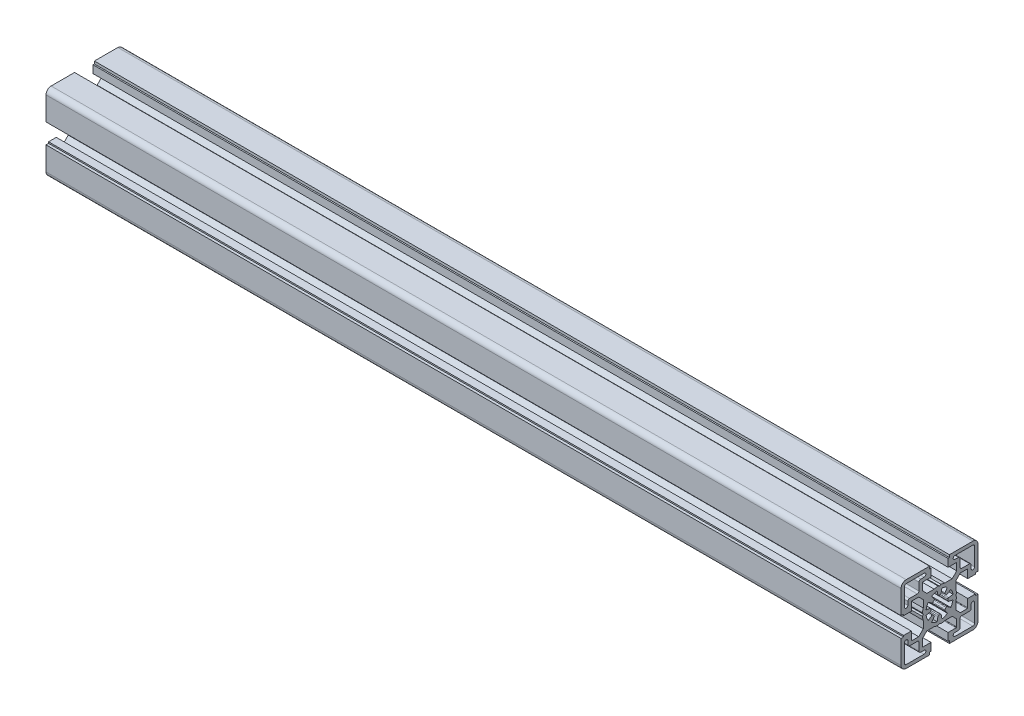
SolidWorks part; units mm, degrees
ref_plane "Спереди" through (0, 0, 0) normal (0, 0, 1) x (1, 0, 0)
ref_plane "Сверху" through (0, 0, 0) normal (0, 1, 0) x (1, 0, 0)
ref_plane "Справа" through (0, 0, 0) normal (1, 0, 0) x (0, 0, -1)
sketch "Эскиз2" plane through (0, 0, 0) normal (1, 0, 0) x (0, 0, -1)
  line L0 (-0.9511, 5.394) -> (-1.3892, 7.8785)
  line L1 (-3.1416, 4.4867) -> (-4.5886, 6.5532)
  line L2 (-4.4867, 3.1416) -> (-6.5532, 4.5886)
  line L3 (7.8785, -1.3892) -> (5.394, -0.9511)
  line L4 (-5.394, 0.9511) -> (-7.8785, 1.3892)
  line L5 (16.5, 5) -> (21, 5)
  line L6 (-21, 5) -> (-16.5, 5)
  line L7 (21, 5.8) -> (22.5, 5.8)
  line L8 (-22.5, 5.8) -> (-21, 5.8)
  line L9 (3.1225, 9.5) -> (7.3787, 9.5)
  line L10 (-7.3787, 9.5) -> (-3.1225, 9.5)
  line L11 (12.1713, 10.05) -> (16.2, 10.05)
  line L12 (-16.2, 10.05) -> (-12.1713, 10.05)
  line L13 (-17.5, 12) -> (-13, 12)
  line L14 (5, 16.5) -> (9.75, 16.5)
  line L15 (-9.75, 16.5) -> (-5, 16.5)
  line L16 (-19.5, 20.5) -> (-9, 20.5)
  line L17 (5, 21) -> (5.8, 21)
  line L18 (-5.8, 21) -> (-5, 21)
  line L19 (5.8, 22.5) -> (19.5, 22.5)
  line L20 (-19.5, 22.5) -> (-5.8, 22.5)
  line L21 (-7.8785, -1.3892) -> (-5.394, -0.9511)
  line L22 (5.394, 0.9511) -> (7.8785, 1.3892)
  line L23 (4.4867, 3.1416) -> (6.5532, 4.5886)
  line L24 (3.1416, 4.4867) -> (4.5886, 6.5532)
  line L25 (0.9511, 5.394) -> (1.3892, 7.8785)
  line L26 (-22.5, 5.8) -> (-22.5, 19.5)
  line L27 (-21, 5) -> (-21, 5.8)
  line L28 (-20.5, 9) -> (-20.5, 19.5)
  line L29 (-16.5, 5) -> (-16.5, 9.75)
  line L30 (-12, 13) -> (-12, 17.5)
  line L31 (-5.8, 21) -> (-5.8, 22.5)
  line L32 (-5, 16.5) -> (-5, 21)
  line L33 (5, 16.5) -> (5, 21)
  line L34 (5.8, 21) -> (5.8, 22.5)
  line L35 (9.5, 3.1225) -> (9.5, 7.3787)
  line L36 (10.05, 12.1713) -> (10.05, 16.2)
  line L37 (16.5, 5) -> (16.5, 9.75)
  line L38 (21, 5) -> (21, 5.8)
  line L39 (22.5, 5.8) -> (22.5, 19.5)
  line L40 (1.3892, -7.8785) -> (0.9511, -5.394)
  line L41 (4.5886, -6.5532) -> (3.1416, -4.4867)
  line L42 (6.5532, -4.5886) -> (4.4867, -3.1416)
  line L43 (-7.3787, -9.5) -> (-3.1225, -9.5)
  line L44 (3.1225, -9.5) -> (7.3787, -9.5)
  line L45 (-6.5532, -4.5886) -> (-4.4867, -3.1416)
  line L46 (-4.5886, -6.5532) -> (-3.1416, -4.4867)
  line L47 (-1.3892, -7.8785) -> (-0.9511, -5.394)
  line L48 (-9.5, -7.3787) -> (-9.5, -3.1225)
  line L49 (9.5, -7.3787) -> (9.5, -3.1225)
  line L50 (-22.5, -5.8) -> (-21, -5.8)
  line L51 (-21, -5) -> (-16.5, -5)
  line L52 (-21, -5.8) -> (-21, -5)
  line L53 (-16.5, -9.75) -> (-16.5, -5)
  line L54 (-22.5, -19.5) -> (-22.5, -5.8)
  line L55 (21, -5.8) -> (22.5, -5.8)
  line L56 (16.5, -5) -> (21, -5)
  line L57 (21, -5.8) -> (21, -5)
  line L58 (16.5, -9.75) -> (16.5, -5)
  line L59 (12.1713, -10.05) -> (16.2, -10.05)
  line L60 (22.5, -19.5) -> (22.5, -5.8)
  line L61 (-16.2, -10.05) -> (-12.1713, -10.05)
  line L62 (5, -16.5) -> (9.75, -16.5)
  line L63 (-9.75, -16.5) -> (-5, -16.5)
  line L64 (5, -21) -> (5.8, -21)
  line L65 (-5.8, -21) -> (-5, -21)
  line L66 (5.8, -22.5) -> (19.5, -22.5)
  line L67 (-19.5, -22.5) -> (-5.8, -22.5)
  line L68 (-10.05, -12.1713) -> (-10.05, -16.2)
  line L69 (-5.8, -21) -> (-5.8, -22.5)
  line L70 (-5, -16.5) -> (-5, -21)
  line L71 (5, -16.5) -> (5, -21)
  line L72 (5.8, -21) -> (5.8, -22.5)
  line L73 (10.05, -12.1713) -> (10.05, -16.2)
  line L74 (-9.5, 3.1225) -> (-9.5, 7.3787)
  line L75 (-9.5, 7.3787) -> (-12.1713, 10.05)
  line L76 (7.3787, 9.5) -> (10.05, 12.1713)
  line L77 (9.5, 7.3787) -> (12.1713, 10.05)
  line L78 (9.5, -7.3787) -> (12.1713, -10.05)
  line L79 (7.3787, -9.5) -> (10.05, -12.1713)
  line L80 (-7.3787, -9.5) -> (-10.05, -12.1713)
  line L81 (-12.1713, -10.05) -> (-9.5, -7.3787)
  line L82 (-10.05, 12.1713) -> (-10.05, 16.2)
  line L83 (-10.05, 12.1713) -> (-7.3787, 9.5)
  line L84 (-9.4624, 0) -> (-9.9624, 0.866)
  line L85 (-9.4624, 0) -> (-9.9624, -0.866)
  line L86 (0, -9.4624) -> (-0.866, -9.9624)
  line L87 (0, -9.4624) -> (0.866, -9.9624)
  line L88 (0, 9.4624) -> (0.866, 9.9624)
  line L89 (0, 9.4624) -> (-0.866, 9.9624)
  line L90 (9.4624, 0) -> (9.9624, -0.866)
  line L91 (9.4624, 0) -> (9.9624, 0.866)
  line L92 (-11, 18.5) -> (-9, 18.5)
  line L93 (-18.5, 11) -> (-18.5, 9)
  line L94 (17.5, 12) -> (13, 12)
  line L95 (12, 13) -> (12, 17.5)
  line L96 (19.5, 20.5) -> (9, 20.5)
  line L97 (11, 18.5) -> (9, 18.5)
  line L98 (20.5, 9) -> (20.5, 19.5)
  line L99 (18.5, 11) -> (18.5, 9)
  line L100 (-17.5, -12) -> (-13, -12)
  line L101 (-12, -13) -> (-12, -17.5)
  line L102 (-19.5, -20.5) -> (-9, -20.5)
  line L103 (-11, -18.5) -> (-9, -18.5)
  line L104 (-20.5, -9) -> (-20.5, -19.5)
  line L105 (-18.5, -11) -> (-18.5, -9)
  line L106 (19.5, -20.5) -> (9, -20.5)
  line L107 (11, -18.5) -> (9, -18.5)
  line L108 (17.5, -12) -> (13, -12)
  line L109 (12, -13) -> (12, -17.5)
  line L110 (20.5, -9) -> (20.5, -19.5)
  line L111 (18.5, -11) -> (18.5, -9)
  arc A0 (-19.5, 20.5) -> (-20.5, 19.5) centre (-19.5, 19.5) ccw
  arc A1 (-19.5, 22.5) -> (-22.5, 19.5) centre (-19.5, 19.5) ccw
  arc A2 (-13, 12) -> (-12, 13) centre (-13, 13) ccw
  arc A3 (-3.2283, 3.8181) -> (-3.8181, 3.2283) centre (0, 0) ccw
  arc A4 (3.8181, 3.2283) -> (3.2283, 3.8181) centre (0, 0) ccw
  arc A5 (-4.9826, 0.417) -> (-4.9826, -0.417) centre (0, 0) ccw
  arc A6 (0.417, 4.9826) -> (-0.417, 4.9826) centre (0, 0) ccw
  arc A7 (4.9826, -0.417) -> (4.9826, 0.417) centre (0, 0) ccw
  arc A8 (-6.5532, 4.5886) -> (-7.8785, 1.3892) centre (0, 0) ccw
  arc A9 (-1.3892, 7.8785) -> (-4.5886, 6.5532) centre (0, 0) ccw
  arc A10 (4.5886, 6.5532) -> (1.3892, 7.8785) centre (0, 0) ccw
  arc A11 (7.8785, 1.3892) -> (6.5532, 4.5886) centre (0, 0) ccw
  arc A12 (22.5, 19.5) -> (19.5, 22.5) centre (19.5, 19.5) ccw
  arc A13 (3.2283, -3.8181) -> (3.8181, -3.2283) centre (0, 0) ccw
  arc A14 (-3.8181, -3.2283) -> (-3.2283, -3.8181) centre (0, 0) ccw
  arc A15 (-0.417, -4.9826) -> (0.417, -4.9826) centre (0, 0) ccw
  arc A16 (6.5532, -4.5886) -> (7.8785, -1.3892) centre (0, 0) ccw
  arc A17 (1.3892, -7.8785) -> (4.5886, -6.5532) centre (0, 0) ccw
  arc A18 (-4.5886, -6.5532) -> (-1.3892, -7.8785) centre (0, 0) ccw
  arc A19 (-7.8785, -1.3892) -> (-6.5532, -4.5886) centre (0, 0) ccw
  arc A20 (-22.5, -19.5) -> (-19.5, -22.5) centre (-19.5, -19.5) ccw
  arc A21 (19.5, -22.5) -> (22.5, -19.5) centre (19.5, -19.5) ccw
  arc A22 (-4.4867, 3.1416) -> (-3.8181, 3.2283) centre (-4.1999, 3.5512) ccw
  arc A23 (-3.2283, 3.8181) -> (-3.1416, 4.4867) centre (-3.5512, 4.1999) ccw
  arc A24 (-0.9511, 5.394) -> (-0.417, 4.9826) centre (-0.4587, 5.4808) ccw
  arc A25 (0.417, 4.9826) -> (0.9511, 5.394) centre (0.4587, 5.4808) ccw
  arc A26 (3.1416, 4.4867) -> (3.2283, 3.8181) centre (3.5512, 4.1999) ccw
  arc A27 (3.8181, 3.2283) -> (4.4867, 3.1416) centre (4.1999, 3.5512) ccw
  arc A28 (5.394, 0.9511) -> (4.9826, 0.417) centre (5.4808, 0.4587) ccw
  arc A29 (4.9826, -0.417) -> (5.394, -0.9511) centre (5.4808, -0.4587) ccw
  arc A30 (4.4867, -3.1416) -> (3.8181, -3.2283) centre (4.1999, -3.5512) ccw
  arc A31 (3.2283, -3.8181) -> (3.1416, -4.4867) centre (3.5512, -4.1999) ccw
  arc A32 (0.9511, -5.394) -> (0.417, -4.9826) centre (0.4587, -5.4808) ccw
  arc A33 (-0.417, -4.9826) -> (-0.9511, -5.394) centre (-0.4587, -5.4808) ccw
  arc A34 (-3.1416, -4.4867) -> (-3.2283, -3.8181) centre (-3.5512, -4.1999) ccw
  arc A35 (-3.8181, -3.2283) -> (-4.4867, -3.1416) centre (-4.1999, -3.5512) ccw
  arc A36 (-5.394, -0.9511) -> (-4.9826, -0.417) centre (-5.4808, -0.4587) ccw
  arc A37 (-4.9826, 0.417) -> (-5.394, 0.9511) centre (-5.4808, 0.4587) ccw
  arc A38 (-16.5, -9.75) -> (-16.2, -10.05) centre (-16.2, -9.75) ccw
  arc A39 (-10.05, -16.2) -> (-9.75, -16.5) centre (-9.75, -16.2) ccw
  arc A40 (9.75, -16.5) -> (10.05, -16.2) centre (9.75, -16.2) ccw
  arc A41 (16.2, -10.05) -> (16.5, -9.75) centre (16.2, -9.75) ccw
  arc A42 (16.5, 9.75) -> (16.2, 10.05) centre (16.2, 9.75) ccw
  arc A43 (10.05, 16.2) -> (9.75, 16.5) centre (9.75, 16.2) ccw
  arc A44 (-9.75, 16.5) -> (-10.05, 16.2) centre (-9.75, 16.2) ccw
  arc A45 (-16.2, 10.05) -> (-16.5, 9.75) centre (-16.2, 9.75) ccw
  arc A46 (-9.9624, -0.866) -> (-9.5, -3.1225) centre (0, 0) ccw
  arc A47 (-9.5, 3.1225) -> (-9.9624, 0.866) centre (0, 0) ccw
  arc A48 (-3.1225, -9.5) -> (-0.866, -9.9624) centre (0, 0) ccw
  arc A49 (3.1225, 9.5) -> (0.866, 9.9624) centre (0, 0) ccw
  arc A50 (9.5, -3.1225) -> (9.9624, -0.866) centre (0, 0) ccw
  arc A51 (-0.866, 9.9624) -> (-3.1225, 9.5) centre (0, 0) ccw
  arc A52 (9.9624, 0.866) -> (9.5, 3.1225) centre (0, 0) ccw
  arc A53 (0.866, -9.9624) -> (3.1225, -9.5) centre (0, 0) ccw
  arc A54 (-11, 18.5) -> (-12, 17.5) centre (-11, 17.5) ccw
  arc A55 (-9, 18.5) -> (-9, 20.5) centre (-9, 19.5) ccw
  arc A56 (-17.5, 12) -> (-18.5, 11) centre (-17.5, 11) ccw
  arc A57 (-20.5, 9) -> (-18.5, 9) centre (-19.5, 9) ccw
  arc A58 (20.5, 19.5) -> (19.5, 20.5) centre (19.5, 19.5) ccw
  arc A59 (12, 13) -> (13, 12) centre (13, 13) ccw
  arc A60 (12, 17.5) -> (11, 18.5) centre (11, 17.5) ccw
  arc A61 (18.5, 11) -> (17.5, 12) centre (17.5, 11) ccw
  arc A62 (9, 20.5) -> (9, 18.5) centre (9, 19.5) ccw
  arc A63 (18.5, 9) -> (20.5, 9) centre (19.5, 9) ccw
  arc A64 (-20.5, -19.5) -> (-19.5, -20.5) centre (-19.5, -19.5) ccw
  arc A65 (-12, -13) -> (-13, -12) centre (-13, -13) ccw
  arc A66 (-12, -17.5) -> (-11, -18.5) centre (-11, -17.5) ccw
  arc A67 (-18.5, -11) -> (-17.5, -12) centre (-17.5, -11) ccw
  arc A68 (-9, -20.5) -> (-9, -18.5) centre (-9, -19.5) ccw
  arc A69 (-18.5, -9) -> (-20.5, -9) centre (-19.5, -9) ccw
  arc A70 (19.5, -20.5) -> (20.5, -19.5) centre (19.5, -19.5) ccw
  arc A71 (11, -18.5) -> (12, -17.5) centre (11, -17.5) ccw
  arc A72 (9, -18.5) -> (9, -20.5) centre (9, -19.5) ccw
  arc A73 (13, -12) -> (12, -13) centre (13, -13) ccw
  arc A74 (17.5, -12) -> (18.5, -11) centre (17.5, -11) ccw
  arc A75 (20.5, -9) -> (18.5, -9) centre (19.5, -9) ccw
  dimension "D1" = 6
  dimension "D2" = 10
  dimension "D3" = 20.1
  dimension "D4" = 4.3287
extrude "Бобышка-Вытянуть1" add sketch "Эскиз2" along normal blind 500 contours L75 L12 A45 L29 L6 L27 L8 L26 A1 L20 L31 L18 L32 L15 A44 L82 L83 L10 A51 L89 L88 A49 L9 L76 L36 A43 L14 L33 L17 L34 L19 A12 L39 L7 L38 L5 L37 A42 L11 L77 L35 A52 L91 L90 A50 L49 L78 L59 A41 L58 L56 L57 L55 L60 A21 L66 L72 L64 L71 L62 A40 L73 L79 L44 A53 L87 L86 A48 L43 L80 L68 A39 L63 L70 L65 L69 L67 A20 L54 L50 L52 L51 L53 A38 L61 L81 L48 A46 L85 L84 A47 L74
sketch "Эскиз3" plane through (0, 0, 0) normal (-1, 0, 0) x (0, 0, 1)
  line L0 (-0.9511, 5.394) -> (-1.3892, 7.8785)
  line L1 (-3.1416, 4.4867) -> (-4.5886, 6.5532)
  line L2 (-4.4867, 3.1416) -> (-6.5532, 4.5886)
  line L3 (7.8785, -1.3892) -> (5.394, -0.9511)
  line L4 (-5.394, 0.9511) -> (-7.8785, 1.3892)
  line L13 (-17.5, 12) -> (-13, 12)
  line L16 (-19.5, 20.5) -> (-9, 20.5)
  line L21 (-7.8785, -1.3892) -> (-5.394, -0.9511)
  line L22 (5.394, 0.9511) -> (7.8785, 1.3892)
  line L23 (4.4867, 3.1416) -> (6.5532, 4.5886)
  line L24 (3.1416, 4.4867) -> (4.5886, 6.5532)
  line L25 (0.9511, 5.394) -> (1.3892, 7.8785)
  line L28 (-20.5, 9) -> (-20.5, 19.5)
  line L30 (-12, 13) -> (-12, 17.5)
  line L40 (1.3892, -7.8785) -> (0.9511, -5.394)
  line L41 (4.5886, -6.5532) -> (3.1416, -4.4867)
  line L42 (6.5532, -4.5886) -> (4.4867, -3.1416)
  line L45 (-6.5532, -4.5886) -> (-4.4867, -3.1416)
  line L46 (-4.5886, -6.5532) -> (-3.1416, -4.4867)
  line L47 (-1.3892, -7.8785) -> (-0.9511, -5.394)
  line L92 (-11, 18.5) -> (-9, 18.5)
  line L93 (-18.5, 11) -> (-18.5, 9)
  line L94 (17.5, 12) -> (13, 12)
  line L95 (12, 13) -> (12, 17.5)
  line L96 (19.5, 20.5) -> (9, 20.5)
  line L97 (11, 18.5) -> (9, 18.5)
  line L98 (20.5, 9) -> (20.5, 19.5)
  line L99 (18.5, 11) -> (18.5, 9)
  line L100 (-17.5, -12) -> (-13, -12)
  line L101 (-12, -13) -> (-12, -17.5)
  line L102 (-19.5, -20.5) -> (-9, -20.5)
  line L103 (-11, -18.5) -> (-9, -18.5)
  line L104 (-20.5, -9) -> (-20.5, -19.5)
  line L105 (-18.5, -11) -> (-18.5, -9)
  line L106 (19.5, -20.5) -> (9, -20.5)
  line L107 (11, -18.5) -> (9, -18.5)
  line L108 (17.5, -12) -> (13, -12)
  line L109 (12, -13) -> (12, -17.5)
  line L110 (20.5, -9) -> (20.5, -19.5)
  line L111 (18.5, -11) -> (18.5, -9)
  arc A0 (-19.5, 20.5) -> (-20.5, 19.5) centre (-19.5, 19.5) ccw
  arc A2 (-13, 12) -> (-12, 13) centre (-13, 13) ccw
  arc A3 (-3.2283, 3.8181) -> (-3.8181, 3.2283) centre (0, 0) ccw
  arc A4 (3.8181, 3.2283) -> (3.2283, 3.8181) centre (0, 0) ccw
  arc A5 (-4.9826, 0.417) -> (-4.9826, -0.417) centre (0, 0) ccw
  arc A6 (0.417, 4.9826) -> (-0.417, 4.9826) centre (0, 0) ccw
  arc A7 (4.9826, -0.417) -> (4.9826, 0.417) centre (0, 0) ccw
  arc A8 (-6.5532, 4.5886) -> (-7.8785, 1.3892) centre (0, 0) ccw
  arc A9 (-1.3892, 7.8785) -> (-4.5886, 6.5532) centre (0, 0) ccw
  arc A10 (4.5886, 6.5532) -> (1.3892, 7.8785) centre (0, 0) ccw
  arc A11 (7.8785, 1.3892) -> (6.5532, 4.5886) centre (0, 0) ccw
  arc A13 (3.2283, -3.8181) -> (3.8181, -3.2283) centre (0, 0) ccw
  arc A14 (-3.8181, -3.2283) -> (-3.2283, -3.8181) centre (0, 0) ccw
  arc A15 (-0.417, -4.9826) -> (0.417, -4.9826) centre (0, 0) ccw
  arc A16 (6.5532, -4.5886) -> (7.8785, -1.3892) centre (0, 0) ccw
  arc A17 (1.3892, -7.8785) -> (4.5886, -6.5532) centre (0, 0) ccw
  arc A18 (-4.5886, -6.5532) -> (-1.3892, -7.8785) centre (0, 0) ccw
  arc A19 (-7.8785, -1.3892) -> (-6.5532, -4.5886) centre (0, 0) ccw
  arc A22 (-4.4867, 3.1416) -> (-3.8181, 3.2283) centre (-4.1999, 3.5512) ccw
  arc A23 (-3.2283, 3.8181) -> (-3.1416, 4.4867) centre (-3.5512, 4.1999) ccw
  arc A24 (-0.9511, 5.394) -> (-0.417, 4.9826) centre (-0.4587, 5.4808) ccw
  arc A25 (0.417, 4.9826) -> (0.9511, 5.394) centre (0.4587, 5.4808) ccw
  arc A26 (3.1416, 4.4867) -> (3.2283, 3.8181) centre (3.5512, 4.1999) ccw
  arc A27 (3.8181, 3.2283) -> (4.4867, 3.1416) centre (4.1999, 3.5512) ccw
  arc A28 (5.394, 0.9511) -> (4.9826, 0.417) centre (5.4808, 0.4587) ccw
  arc A29 (4.9826, -0.417) -> (5.394, -0.9511) centre (5.4808, -0.4587) ccw
  arc A30 (4.4867, -3.1416) -> (3.8181, -3.2283) centre (4.1999, -3.5512) ccw
  arc A31 (3.2283, -3.8181) -> (3.1416, -4.4867) centre (3.5512, -4.1999) ccw
  arc A32 (0.9511, -5.394) -> (0.417, -4.9826) centre (0.4587, -5.4808) ccw
  arc A33 (-0.417, -4.9826) -> (-0.9511, -5.394) centre (-0.4587, -5.4808) ccw
  arc A34 (-3.1416, -4.4867) -> (-3.2283, -3.8181) centre (-3.5512, -4.1999) ccw
  arc A35 (-3.8181, -3.2283) -> (-4.4867, -3.1416) centre (-4.1999, -3.5512) ccw
  arc A36 (-5.394, -0.9511) -> (-4.9826, -0.417) centre (-5.4808, -0.4587) ccw
  arc A37 (-4.9826, 0.417) -> (-5.394, 0.9511) centre (-5.4808, 0.4587) ccw
  arc A54 (-11, 18.5) -> (-12, 17.5) centre (-11, 17.5) ccw
  arc A55 (-9, 18.5) -> (-9, 20.5) centre (-9, 19.5) ccw
  arc A56 (-17.5, 12) -> (-18.5, 11) centre (-17.5, 11) ccw
  arc A57 (-20.5, 9) -> (-18.5, 9) centre (-19.5, 9) ccw
  arc A58 (20.5, 19.5) -> (19.5, 20.5) centre (19.5, 19.5) ccw
  arc A59 (12, 13) -> (13, 12) centre (13, 13) ccw
  arc A60 (12, 17.5) -> (11, 18.5) centre (11, 17.5) ccw
  arc A61 (18.5, 11) -> (17.5, 12) centre (17.5, 11) ccw
  arc A62 (9, 20.5) -> (9, 18.5) centre (9, 19.5) ccw
  arc A63 (18.5, 9) -> (20.5, 9) centre (19.5, 9) ccw
  arc A64 (-20.5, -19.5) -> (-19.5, -20.5) centre (-19.5, -19.5) ccw
  arc A65 (-12, -13) -> (-13, -12) centre (-13, -13) ccw
  arc A66 (-12, -17.5) -> (-11, -18.5) centre (-11, -17.5) ccw
  arc A67 (-18.5, -11) -> (-17.5, -12) centre (-17.5, -11) ccw
  arc A68 (-9, -20.5) -> (-9, -18.5) centre (-9, -19.5) ccw
  arc A69 (-18.5, -9) -> (-20.5, -9) centre (-19.5, -9) ccw
  arc A70 (19.5, -20.5) -> (20.5, -19.5) centre (19.5, -19.5) ccw
  arc A71 (11, -18.5) -> (12, -17.5) centre (11, -17.5) ccw
  arc A72 (9, -18.5) -> (9, -20.5) centre (9, -19.5) ccw
  arc A73 (13, -12) -> (12, -13) centre (13, -13) ccw
  arc A74 (17.5, -12) -> (18.5, -11) centre (17.5, -11) ccw
  arc A75 (20.5, -9) -> (18.5, -9) centre (19.5, -9) ccw
extrude "Вырез-Вытянуть1" cut sketch "Эскиз3" against normal through all
